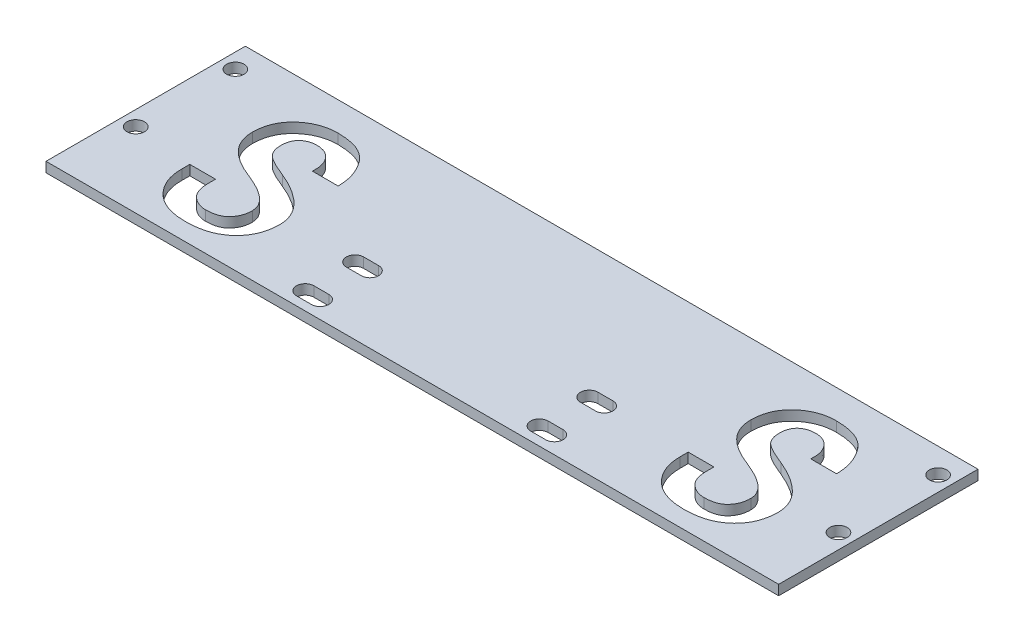
SolidWorks part; units mm, degrees
ref_plane "前视基准面" through (0, 0, 0) normal (0, 0, 1) x (1, 0, 0)
ref_plane "上视基准面" through (0, 0, 0) normal (0, 1, 0) x (1, 0, 0)
ref_plane "右视基准面" through (0, 0, 0) normal (1, 0, 0) x (0, 0, -1)
sketch "草图1" plane through (0, 0, 0) normal (0, 1, 0) x (1, 0, 0)
  line L1 (-73.5, 31) -> (73.5, 31)
  line L2 (-73.5, 31) -> (-73.5, -31)
  line L3 (-73.5, -31) -> (73.5, -31)
  line L4 (73.5, 31) -> (73.5, -31)
  line L5 (-73.5, 31) -> (73.5, -31) construction
  line L6 (-73.5, -31) -> (73.5, 31) construction
  point P0 (0, 0)
  dimension "D1" = 147
  dimension "D2" = 62
extrude "凸台-拉伸1" add sketch "草图1" along normal blind 2
sketch "草图2" plane through (0, 2, 0) normal (0, 1, 0) x (1, 0, 0)
  line L0 (25, 4.5) -> (22, 4.5) construction
  line L1 (25, 2.75) -> (22, 2.75)
  line L2 (25, 6.25) -> (22, 6.25)
  line L3 (25, -5.5) -> (22, -5.5) construction
  line L4 (25, -7.25) -> (22, -7.25)
  line L5 (25, -3.75) -> (22, -3.75)
  line L6 (-25, 4.5) -> (-22, 4.5) construction
  line L7 (-25, 6.25) -> (-22, 6.25)
  line L8 (-25, 2.75) -> (-22, 2.75)
  line L9 (-25, -5.5) -> (-22, -5.5) construction
  line L10 (-25, -3.75) -> (-22, -3.75)
  line L11 (-25, -7.25) -> (-22, -7.25)
  line L12 (70.5, 26) -> (70.5, 6) construction
  line L13 (73.5, -31) -> (73.5, 31) construction
  line L14 (73.5, 31) -> (-73.5, 31) construction
  line L15 (-70.5, 26) -> (-70.5, 6) construction
  line L16 (-73.5, 31) -> (-73.5, -31) construction
  arc A0 (25, 2.75) -> (25, 6.25) centre (25, 4.5) ccw
  arc A1 (22, 6.25) -> (22, 2.75) centre (22, 4.5) ccw
  arc A2 (25, -7.25) -> (25, -3.75) centre (25, -5.5) ccw
  arc A3 (22, -3.75) -> (22, -7.25) centre (22, -5.5) ccw
  arc A4 (-25, 6.25) -> (-25, 2.75) centre (-25, 4.5) ccw
  arc A5 (-22, 2.75) -> (-22, 6.25) centre (-22, 4.5) ccw
  arc A6 (-25, -3.75) -> (-25, -7.25) centre (-25, -5.5) ccw
  arc A7 (-22, -7.25) -> (-22, -3.75) centre (-22, -5.5) ccw
  circle A8 centre (70.5, 26) radius 1.75
  circle A9 centre (70.5, 6) radius 1.75
  circle A10 centre (-70.5, 6) radius 1.75
  circle A11 centre (-70.5, 26) radius 1.75
  point P3 (23.5, 4.5)
  point P8 (23.5, -5.5)
  point P16 (-23.5, 4.5)
  point P24 (-23.5, -5.5)
  dimension "D1" = 1.75
  dimension "D3" = 3.5
  dimension "D6" = 5
  dimension "D8" = 3
  dimension "D2" = 3
  dimension "D4" = 3
  dimension "D5" = 20
  dimension "D7" = 20
  dimension "D9" = 5
extrude "切除-拉伸1" cut sketch "草图2" against normal through all
sketch "草图3" plane through (0, 2, 0) normal (0, 1, 0) x (1, 0, 0)
  line L0 (-30, 9.5) -> (30, 9.5) construction
  line L1 (-25, 4.5) -> (25, 4.5) construction
  line L2 (-25, 4.5) -> (-25, -5.5) construction
  line L3 (-25, -5.5) -> (25, -5.5) construction
  line L4 (25, 4.5) -> (25, -5.5) construction
  line L5 (30, 9.5) -> (30, -10.5) construction
  line L6 (-30, -10.5) -> (30, -10.5) construction
  line L7 (-30, 9.5) -> (-30, -10.5) construction
  line L8 (-20, -0.5) -> (20, -0.5) construction
  line L9 (20, -0.5) -> (20, -0.5) construction
  line L10 (-20, -0.5) -> (20, -0.5) construction
  line L11 (-20, -0.5) -> (-20, -0.5) construction
  line L12 (-73.5, 31) -> (-73.5, -31) construction
  line L13 (-67.5, 29) -> (-73.5, 29) construction
  line L14 (-67.5, 29) -> (-67.5, 23) construction
  line L15 (-67.5, 23) -> (-73.5, 23) construction
  line L16 (-73.5, 29) -> (-73.5, 23) construction
  line L17 (-67.5, 29) -> (-73.5, 23) construction
  line L18 (-67.5, 23) -> (-73.5, 29) construction
  line L19 (73.5, -31) -> (73.5, 31) construction
  line L20 (-67.5, 9) -> (-73.5, 9) construction
  line L21 (-67.5, 9) -> (-67.5, 3) construction
  line L22 (-67.5, 3) -> (-73.5, 3) construction
  line L23 (-73.5, 9) -> (-73.5, 3) construction
  line L24 (-67.5, 9) -> (-73.5, 3) construction
  line L25 (-67.5, 3) -> (-73.5, 9) construction
  line L26 (67.5, 29) -> (73.5, 29) construction
  line L27 (67.5, 29) -> (67.5, 23) construction
  line L28 (67.5, 23) -> (73.5, 23) construction
  line L29 (73.5, 29) -> (73.5, 23) construction
  line L30 (67.5, 29) -> (73.5, 23) construction
  line L31 (67.5, 23) -> (73.5, 29) construction
  line L33 (67.5, 9) -> (73.5, 9) construction
  line L34 (67.5, 9) -> (67.5, 3) construction
  line L35 (67.5, 3) -> (73.5, 3) construction
  line L36 (73.5, 9) -> (73.5, 3) construction
  line L37 (67.5, 9) -> (73.5, 3)
  line L38 (67.5, 3) -> (73.5, 9)
  point P14 (-70.5, 26)
  point P22 (-70.5, 6)
  point P28 (70.5, 26)
  point P36 (70.5, 6)
  dimension "D1" = 5
  dimension "D2" = 5
sketch "草图4" plane through (0, 2, 0) normal (0, 1, 0) x (1, 0, 0)
  line L0 (-30, -6) -> (-67.5, -6) construction
  line L1 (-73.5, -31) -> (73.5, -31) construction
  line L4 (-67.5, -6) -> (-67.5, 3) construction
  text T0 "S" font "黑体" height 30
  dimension "D1" = 25
extrude "切除-拉伸2" cut sketch "草图4" against normal through all
pattern_linear "阵列(线性)1" count 2 spacing 100 along (1, 0, 0) of "切除-拉伸2"
sketch "草图5" plane through (0, 2, 0) normal (0, 1, 0) x (1, 0, 0)
  line L0 (-73.5, -31) -> (-73.5, -19)
  line L1 (-73.5, 31) -> (-73.5, -31) construction
  line L2 (-73.5, -19) -> (73.5, -19)
  line L3 (73.5, -31) -> (73.5, 31) construction
  line L4 (73.5, -19) -> (73.5, -31)
  line L5 (73.5, -31) -> (-73.5, -31)
  dimension "D1" = 12
extrude "切除-拉伸3" cut sketch "草图5" against normal blind 10
sketch "草图6" plane through (0, 2, 0) normal (0, 1, 0) x (1, 0, 0)
  line L0 (73.5, -19) -> (73.5, 31) construction
  line L1 (-73.5, -19) -> (73.5, -19)
  line L2 (-73.5, -19) -> (-73.5, -9)
  line L3 (-73.5, -9) -> (73.5, -9)
  line L4 (73.5, -19) -> (73.5, -9)
  dimension "D1" = 10
extrude "切除-拉伸4" cut sketch "草图6" against normal through all
